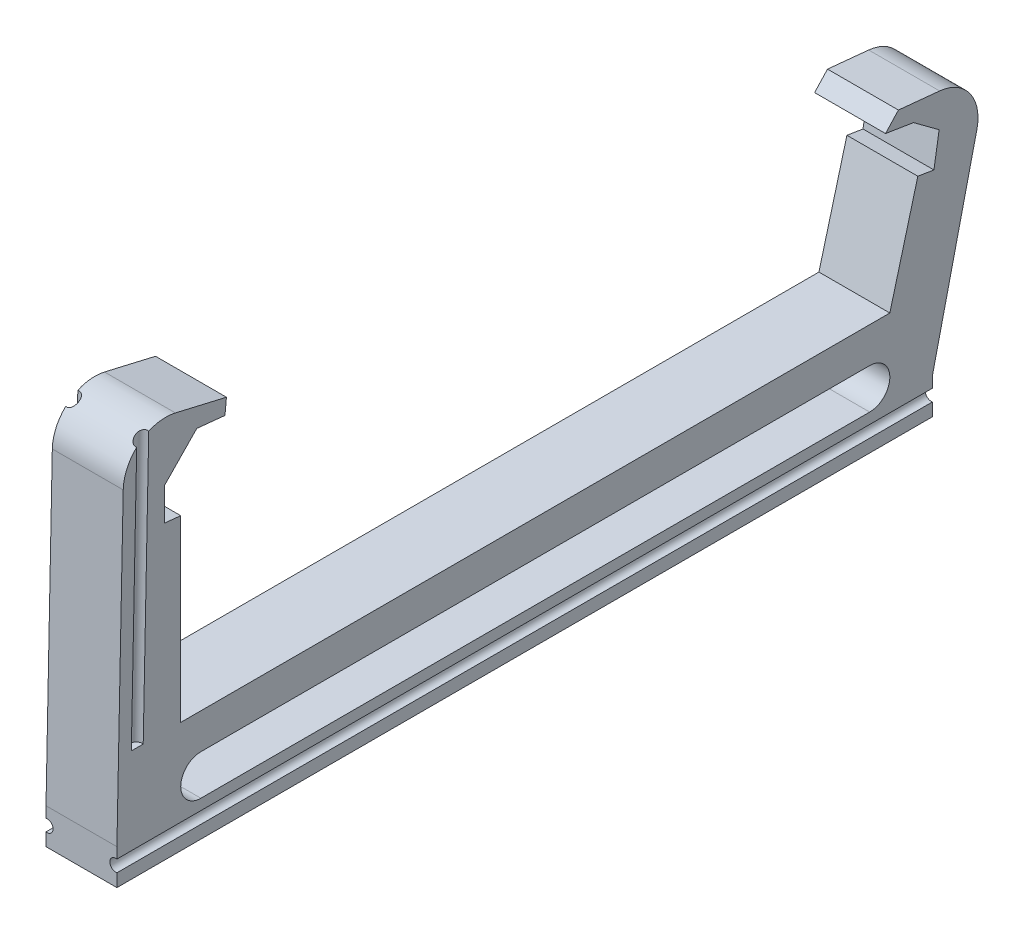
SolidWorks part; units mm, degrees
ref_plane "Front Plane" through (0, 0, 0) normal (0, 0, 1) x (1, 0, 0)
ref_plane "Top Plane" through (0, 0, 0) normal (0, 1, 0) x (1, 0, 0)
ref_plane "Right Plane" through (0, 0, 0) normal (1, 0, 0) x (0, 0, -1)
sketch "Sketch1" plane through (0, 0, 0) normal (1, 0, 0) x (0, 0, -1)
  line L0 (0, 35) -> (0, 0) construction
  line L1 (0, 0) -> (100, 0)
  line L2 (100, 0) -> (105.6811, 21.2021) construction
  line L3 (0, 35) -> (6.2429, 34.3659) construction
  line L4 (105.6811, 21.2021) -> (99.393, 22.2205) construction
  line L5 (6.2429, 34.3659) -> (6.4453, 36.4946)
  line L6 (6.4453, 36.4946) -> (-0.7519, 38.1708)
  line L7 (-8.1116, 32.4507) -> (-9, -10.68)
  line L8 (-9, -10.68) -> (106, -10.68) construction
  line L9 (106, -10.68) -> (112.278, 16.2769)
  line L10 (107.021, 23.6091) -> (101.2106, 24.1798)
  line L11 (101.2106, 24.1798) -> (99.393, 22.2205)
  line L12 (0, 0) -> (0, -10.68) construction
  line L13 (2.84, -7.84) -> (97.16, -7.84) construction
  line L14 (2.84, -5) -> (97.16, -5)
  line L15 (2.84, -10.68) -> (97.16, -10.68)
  line L16 (-9, -10.68) -> (-9, -15.68)
  line L17 (-9, -15.68) -> (106, -15.68)
  line L18 (106, -15.68) -> (106, -10.68)
  line L19 (6.2429, 34.3659) -> (2.2634, 34.7701)
  line L20 (0, 25.25) -> (-2.2882, 25.4824)
  line L21 (-2.2882, 25.4824) -> (-2.2882, 30.0824)
  line L22 (-2.2882, 30.0824) -> (2.2634, 34.7701)
  line L23 (0, 25.25) -> (0, 35) construction
  line L24 (0, 25.25) -> (0, 0)
  line L25 (100, 0) -> (103.947, 14.7304)
  line L26 (103.947, 14.7304) -> (106.2174, 14.3626)
  line L27 (106.2174, 14.3626) -> (106.9529, 18.9035)
  line L28 (106.9529, 18.9035) -> (103.3416, 21.581)
  line L29 (103.3416, 21.581) -> (99.393, 22.2205)
  arc A0 (2.84, -5) -> (2.84, -10.68) centre (2.84, -7.84) ccw
  arc A1 (97.16, -10.68) -> (97.16, -5) centre (97.16, -7.84) ccw
  arc A2 (112.278, 16.2769) -> (107.021, 23.6091) centre (106.4344, 17.6378) ccw
  arc A3 (-0.7519, 38.1708) -> (-8.1116, 32.4507) centre (-2.1129, 32.3272) ccw
  point P3 (50, -7.84)
  point P22 (50, 0)
  point P26 (113.8299, 22.9403)
  point P29 (-7.9592, 39.8493)
  dimension "D22" = 6
  dimension "D1" = 35
  dimension "D2" = 100
  dimension "D3" = 21.95
  dimension "D4" = 105
  dimension "D5" = 84.2
  dimension "D6" = 6.37
  dimension "D7" = 84.2
  dimension "D8" = 6.275
  dimension "D9" = 115
  dimension "D10" = 50.54
  dimension "D11" = 34.52
  dimension "D12" = 10.68
  dimension "D13" = 103.11
  dimension "D14" = 88.82
  dimension "D15" = 9
  dimension "D16" = 12.68
  dimension "D17" = 82.5
  dimension "D18" = 14.79
  dimension "D19" = 78.07
  dimension "D20" = 5
  dimension "D21" = 5
  dimension "D23" = 2.3
  dimension "D24" = 4.6
  dimension "D25" = 4
  dimension "D26" = 25.25
  dimension "D27" = 2.3
  dimension "D28" = 4.6
  dimension "D29" = 4
  dimension "D30" = 15.25
  dimension "D31" = 95.8
  dimension "D32" = 95.8
extrude "Boss-Extrude1" add sketch "Sketch1" along normal blind 10
ref_plane "Plane1" through (0, 38.2687, -0.7883) normal (0, 0.9998, -0.0206) x (1, 0, 0)
sketch "Sketch2" plane through (0, 38.2687, -0.7883) normal (0, 0.9998, -0.0206) x (1, 0, 0)
  line L0 (0, -8.7782) -> (10, -8.7782)
  line L1 (10, -8.7782) -> (10, 5.6924)
  line L2 (10, 5.6924) -> (0, 5.6924)
  line L3 (0, 5.6924) -> (0, -8.7782)
  line L4 (5, -8.7782) -> (5, 5.6924) construction
  arc A0 (0, -6.9648) -> (0, -5.2915) centre (0.15, -6.1282) ccw
  arc A1 (10, -6.9648) -> (10, -5.2915) centre (9.85, -6.1282) cw
  dimension "D2" = 0.85
  dimension "D1" = 0.15
  dimension "D3" = 2.65
ref_plane "Plane2" through (0, 0, 0) normal (0, 1, 0) x (1, 0, 0)
extrude "Cut-Extrude4" cut sketch "Sketch2" against normal up to surface (38.4202 mm away) contours L3 A0 up to plane "Plane2"
ref_plane "Plane3" through (5, 0, 0) normal (1, 0, 0) x (0, 0, -1)
mirror "Mirror1" about plane through (5, 0, 0) normal (1, 0, 0) of "Cut-Extrude4"
sketch "Sketch3" plane through (0, 0, 0) normal (0, 0, 1) x (1, 0, 0)
  line L0 (0, -10.68) -> (0, -15.68)
  line L1 (0, -15.68) -> (0, -10.68) construction
  line L2 (0, -15.68) -> (10, -15.68)
  line L3 (10, -15.68) -> (10, -10.68)
  line L4 (10, -10.68) -> (0, -10.68)
  arc A0 (0, -13.8667) -> (0, -12.1933) centre (0.15, -13.03) ccw
  dimension "D2" = 0.85
  dimension "D1" = 0.15
  dimension "D3" = 2.65
extrude "Cut-Extrude5" cut sketch "Sketch3" against normal through all and the other way through all contours A0
mirror "Mirror2" about plane through (5, 0, 0) normal (1, 0, 0) of "Cut-Extrude5"
